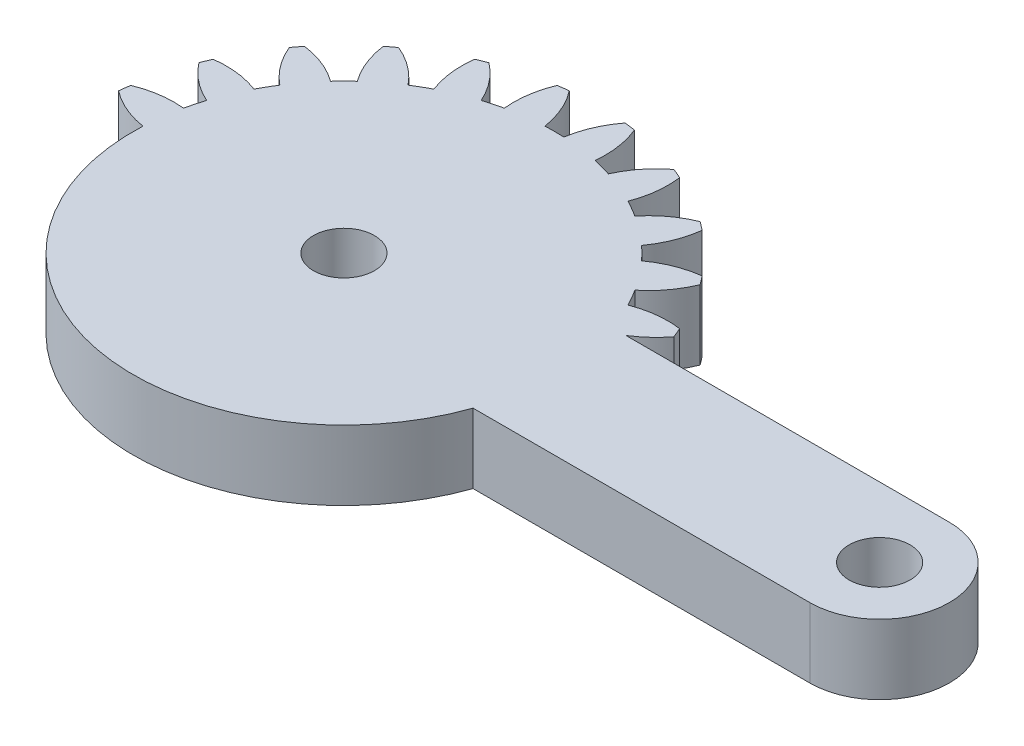
SolidWorks part; units mm, degrees
ref_plane "Front Plane" through (0, 0, 0) normal (0, 0, 1) x (1, 0, 0)
ref_plane "Top Plane" through (0, 0, 0) normal (0, 1, 0) x (1, 0, 0)
ref_plane "Right Plane" through (0, 0, 0) normal (1, 0, 0) x (0, 0, -1)
sketch "Sketch1" plane through (0, 0, 0) normal (0, 1, 0) x (1, 0, 0)
  line L0 (20.6437, 4) -> (2.0816, 4)
  line L1 (2.0816, -4) -> (20.6437, -4)
  arc A0 (2.0816, 4) -> (3.5217, 5.3071) centre (-0.7683, 8.5867) ccw
  arc A1 (3.5217, 5.3071) -> (3.2829, 5.8838) centre (-10.1063, 0) ccw
  arc A2 (3.2829, 5.8838) -> (0.6271, 5.5703) centre (2.5684, 0.5313) ccw
  arc A3 (0.6271, 5.5703) -> (0.0844, 6.5103) centre (-10.1063, 0) ccw
  arc A4 (0.0844, 6.5103) -> (1.6838, 8.6535) centre (-3.3089, 10.711) ccw
  arc A5 (1.6838, 8.6535) -> (1.3038, 9.1487) centre (-10.1063, 0) ccw
  arc A6 (1.3038, 9.1487) -> (-1.1803, 8.1585) centre (1.999, 3.7936) ccw
  arc A7 (-1.1803, 8.1585) -> (-1.9479, 8.926) centre (-10.1063, 0) ccw
  arc A8 (-1.9479, 8.926) -> (-0.9576, 11.4102) centre (-6.3127, 12.1053) ccw
  arc A9 (-0.9576, 11.4102) -> (-1.4528, 11.7901) centre (-10.1063, 0) ccw
  arc A10 (-1.4528, 11.7901) -> (-3.596, 10.1907) centre (0.6046, 6.7975) ccw
  arc A11 (-3.596, 10.1907) -> (-4.5361, 10.7334) centre (-10.1063, 0) ccw
  arc A12 (-4.5361, 10.7334) -> (-4.2225, 13.3892) centre (-9.5751, 12.6747) ccw
  arc A13 (-4.2225, 13.3892) -> (-4.7992, 13.6281) centre (-10.1063, 0) ccw
  arc A14 (-4.7992, 13.6281) -> (-6.4554, 11.5285) centre (-1.5196, 9.3381) ccw
  arc A15 (-6.4554, 11.5285) -> (-7.5039, 11.8094) centre (-10.1063, 0) ccw
  arc A16 (-7.5039, 11.8094) -> (-7.8884, 14.4558) centre (-12.8736, 12.3803) ccw
  arc A17 (-7.8884, 14.4558) -> (-8.5072, 14.5373) centre (-10.1063, 0) ccw
  arc A18 (-8.5072, 14.5373) -> (-9.5636, 12.0806) centre (-4.2291, 11.2423) ccw
  arc A19 (-9.5636, 12.0806) -> (-10.6491, 12.0806) centre (-10.1063, 0) ccw
  arc A20 (-10.6491, 12.0806) -> (-11.7054, 14.5373) centre (-15.9836, 11.2423) ccw
  arc A21 (-11.7054, 14.5373) -> (-12.3243, 14.4558) centre (-10.1063, 0) ccw
  arc A22 (-12.3243, 14.4558) -> (-12.7088, 11.8094) centre (-7.3391, 12.3803) ccw
  arc A23 (-12.7088, 11.8094) -> (-13.7573, 11.5285) centre (-10.1063, 0) ccw
  arc A24 (-13.7573, 11.5285) -> (-15.4135, 13.6281) centre (-18.6931, 9.3381) ccw
  arc A25 (-15.4135, 13.6281) -> (-15.9901, 13.3892) centre (-10.1063, 0) ccw
  arc A26 (-15.9901, 13.3892) -> (-15.6766, 10.7334) centre (-10.6376, 12.6747) ccw
  arc A27 (-15.6766, 10.7334) -> (-16.6166, 10.1907) centre (-10.1063, 0) ccw
  arc A28 (-16.6166, 10.1907) -> (-18.7599, 11.7901) centre (-20.8173, 6.7975) ccw
  arc A29 (-18.7599, 11.7901) -> (-19.255, 11.4102) centre (-10.1063, 0) ccw
  arc A30 (-19.255, 11.4102) -> (-18.2648, 8.926) centre (-13.9, 12.1053) ccw
  arc A31 (-18.2648, 8.926) -> (-19.0324, 8.1585) centre (-10.1063, 0) ccw
  arc A32 (-19.0324, 8.1585) -> (-21.5165, 9.1487) centre (-22.2117, 3.7936) ccw
  arc A33 (-21.5165, 9.1487) -> (-21.8965, 8.6535) centre (-10.1063, 0) ccw
  arc A34 (-21.8965, 8.6535) -> (-20.2971, 6.5103) centre (-16.9038, 10.711) ccw
  arc A35 (-20.2971, 6.5103) -> (-20.8398, 5.5703) centre (-10.1063, 0) ccw
  arc A36 (-20.8398, 5.5703) -> (-23.4956, 5.8838) centre (-22.7811, 0.5313) ccw
  arc A37 (-23.4956, 5.8838) -> (-23.7344, 5.3071) centre (-10.1063, 0) ccw
  arc A38 (-23.7344, 5.3071) -> (-21.6348, 3.6509) centre (-19.4444, 8.5867) ccw
  arc A39 (-21.6348, 3.6509) -> (-21.9157, 2.6025) centre (-10.1063, 0) ccw
  arc A40 (-21.9157, 2.6025) -> (-24.5622, 2.2179) centre (-22.4867, -2.7673) ccw
  arc A41 (-24.5622, 2.2179) -> (-24.6437, 1.5991) centre (-10.1063, 0) ccw
  arc A42 (-24.6437, 1.5991) -> (-22.1869, 0.5427) centre (-21.3486, 5.8773) ccw
  arc A43 (-22.1869, 0.5427) -> (-22.1869, -0.5427) centre (-10.1063, 0) ccw
  arc A44 (-22.1869, -0.5427) -> (-24.6437, -1.5991) centre (-21.3486, -5.8773) ccw
  arc A45 (-24.6437, -1.5991) -> (-24.5622, -2.2179) centre (-10.1063, 0) ccw
  arc A46 (-24.5622, -2.2179) -> (-21.9157, -2.6025) centre (-22.4867, 2.7673) ccw
  arc A47 (-21.9157, -2.6025) -> (-21.6348, -3.6509) centre (-10.1063, 0) ccw
  arc A48 (-21.6348, -3.6509) -> (-23.7344, -5.3071) centre (-19.4444, -8.5867) ccw
  arc A49 (-23.7344, -5.3071) -> (-23.4956, -5.8838) centre (-10.1063, 0) ccw
  arc A50 (-23.4956, -5.8838) -> (-20.8398, -5.5703) centre (-22.7811, -0.5313) ccw
  arc A51 (-20.8398, -5.5703) -> (-20.2971, -6.5103) centre (-10.1063, 0) ccw
  arc A52 (-20.2971, -6.5103) -> (-21.8965, -8.6535) centre (-16.9038, -10.711) ccw
  arc A53 (-21.8965, -8.6535) -> (-21.5165, -9.1487) centre (-10.1063, 0) ccw
  arc A54 (-21.5165, -9.1487) -> (-19.0324, -8.1585) centre (-22.2117, -3.7936) ccw
  arc A55 (-19.0324, -8.1585) -> (-18.2648, -8.926) centre (-10.1063, 0) ccw
  arc A56 (-18.2648, -8.926) -> (-19.255, -11.4102) centre (-13.9, -12.1053) ccw
  arc A57 (-19.255, -11.4102) -> (-18.7599, -11.7901) centre (-10.1063, 0) ccw
  arc A58 (-18.7599, -11.7901) -> (-16.6166, -10.1907) centre (-20.8173, -6.7975) ccw
  arc A59 (-16.6166, -10.1907) -> (-15.6766, -10.7334) centre (-10.1063, 0) ccw
  arc A60 (-15.6766, -10.7334) -> (-15.9901, -13.3892) centre (-10.6376, -12.6747) ccw
  arc A61 (-15.9901, -13.3892) -> (-15.4135, -13.6281) centre (-10.1063, 0) ccw
  arc A62 (-15.4135, -13.6281) -> (-13.7573, -11.5285) centre (-18.6931, -9.3381) ccw
  arc A63 (-13.7573, -11.5285) -> (-12.7088, -11.8094) centre (-10.1063, 0) ccw
  arc A64 (-12.7088, -11.8094) -> (-12.3243, -14.4558) centre (-7.3391, -12.3803) ccw
  arc A65 (-12.3243, -14.4558) -> (-11.7054, -14.5373) centre (-10.1063, 0) ccw
  arc A66 (-11.7054, -14.5373) -> (-10.6491, -12.0806) centre (-15.9836, -11.2423) ccw
  arc A67 (-10.6491, -12.0806) -> (-9.5636, -12.0806) centre (-10.1063, 0) ccw
  arc A68 (-9.5636, -12.0806) -> (-8.5072, -14.5373) centre (-4.2291, -11.2423) ccw
  arc A69 (-8.5072, -14.5373) -> (-7.8884, -14.4558) centre (-10.1063, 0) ccw
  arc A70 (-7.8884, -14.4558) -> (-7.5039, -11.8094) centre (-12.8736, -12.3803) ccw
  arc A71 (-7.5039, -11.8094) -> (-6.4554, -11.5285) centre (-10.1063, 0) ccw
  arc A72 (-6.4554, -11.5285) -> (-4.7992, -13.6281) centre (-1.5196, -9.3381) ccw
  arc A73 (-4.7992, -13.6281) -> (-4.2225, -13.3892) centre (-10.1063, 0) ccw
  arc A74 (-4.2225, -13.3892) -> (-4.5361, -10.7334) centre (-9.5751, -12.6747) ccw
  arc A75 (-4.5361, -10.7334) -> (-3.596, -10.1907) centre (-10.1063, 0) ccw
  arc A76 (-3.596, -10.1907) -> (-1.4528, -11.7901) centre (0.6046, -6.7975) ccw
  arc A77 (-1.4528, -11.7901) -> (-0.9576, -11.4102) centre (-10.1063, 0) ccw
  arc A78 (-0.9576, -11.4102) -> (-1.9479, -8.926) centre (-6.3127, -12.1053) ccw
  arc A79 (-1.9479, -8.926) -> (-1.1803, -8.1585) centre (-10.1063, 0) ccw
  arc A80 (-1.1803, -8.1585) -> (1.3038, -9.1487) centre (1.999, -3.7936) ccw
  arc A81 (1.3038, -9.1487) -> (1.6838, -8.6535) centre (-10.1063, 0) ccw
  arc A82 (1.6838, -8.6535) -> (0.0844, -6.5103) centre (-3.3089, -10.711) ccw
  arc A83 (0.0844, -6.5103) -> (0.6271, -5.5703) centre (-10.1063, 0) ccw
  arc A84 (0.6271, -5.5703) -> (3.2829, -5.8838) centre (2.5684, -0.5313) ccw
  arc A85 (3.2829, -5.8838) -> (3.5217, -5.3071) centre (-10.1063, 0) ccw
  arc A86 (3.5217, -5.3071) -> (2.0816, -4) centre (-0.7683, -8.5867) ccw
  arc A87 (20.6437, -4) -> (20.6437, 4) centre (20.6437, 0) ccw
  circle A88 centre (-10.1063, 0) radius 1.75
  circle A89 centre (20.6437, 0) radius 1.75
  dimension "D1" = 3.5
  dimension "D2" = 3.5
extrude "Boss-Extrude1" add sketch "Sketch1" along normal blind 4
sketch "Sketch2" plane through (0, 4, 0) normal (0, 1, 0) x (1, 0, 0)
  line L0 (2.0816, -4) -> (1.3057, -4)
  line L2 (20.6437, 4) -> (2.0816, 4)
  line L3 (2.0816, -4) -> (20.6437, -4)
  line L4 (20.6437, 4) -> (2.0816, 4)
  line L5 (2.0816, -4) -> (20.6437, -4)
  circle A0 centre (-10.1063, 0) radius 12.0927
  arc A88 (20.6437, -4) -> (20.6437, 4) centre (20.6437, 0) ccw
  arc A89 (2.0816, 4) -> (3.5217, 5.3071) centre (-0.7683, 8.5867) ccw
  arc A90 (3.5217, 5.3071) -> (3.2829, 5.8838) centre (-10.1063, 0) ccw
  arc A91 (3.2829, 5.8838) -> (0.6271, 5.5703) centre (2.5684, 0.5313) ccw
  arc A92 (0.6271, 5.5703) -> (0.0844, 6.5103) centre (-10.1063, 0) ccw
  arc A93 (0.0844, 6.5103) -> (1.6838, 8.6535) centre (-3.3089, 10.711) ccw
  arc A94 (1.6838, 8.6535) -> (1.3038, 9.1487) centre (-10.1063, 0) ccw
  arc A95 (1.3038, 9.1487) -> (-1.1803, 8.1585) centre (1.999, 3.7936) ccw
  arc A96 (-1.1803, 8.1585) -> (-1.9479, 8.926) centre (-10.1063, 0) ccw
  arc A97 (-1.9479, 8.926) -> (-0.9576, 11.4102) centre (-6.3127, 12.1053) ccw
  arc A98 (-0.9576, 11.4102) -> (-1.4528, 11.7901) centre (-10.1063, 0) ccw
  arc A99 (-1.4528, 11.7901) -> (-3.596, 10.1907) centre (0.6046, 6.7975) ccw
  arc A100 (-3.596, 10.1907) -> (-4.5361, 10.7334) centre (-10.1063, 0) ccw
  arc A101 (-4.5361, 10.7334) -> (-4.2225, 13.3892) centre (-9.5751, 12.6747) ccw
  arc A102 (-4.2225, 13.3892) -> (-4.7992, 13.6281) centre (-10.1063, 0) ccw
  arc A103 (-4.7992, 13.6281) -> (-6.4554, 11.5285) centre (-1.5196, 9.3381) ccw
  arc A104 (-6.4554, 11.5285) -> (-7.5039, 11.8094) centre (-10.1063, 0) ccw
  arc A105 (-7.5039, 11.8094) -> (-7.8884, 14.4558) centre (-12.8736, 12.3803) ccw
  arc A106 (-7.8884, 14.4558) -> (-8.5072, 14.5373) centre (-10.1063, 0) ccw
  arc A107 (-8.5072, 14.5373) -> (-9.5636, 12.0806) centre (-4.2291, 11.2423) ccw
  arc A108 (-9.5636, 12.0806) -> (-10.6491, 12.0806) centre (-10.1063, 0) ccw
  arc A109 (-10.6491, 12.0806) -> (-11.7054, 14.5373) centre (-15.9836, 11.2423) ccw
  arc A110 (-11.7054, 14.5373) -> (-12.3243, 14.4558) centre (-10.1063, 0) ccw
  arc A111 (-12.3243, 14.4558) -> (-12.7088, 11.8094) centre (-7.3391, 12.3803) ccw
  arc A112 (-12.7088, 11.8094) -> (-13.7573, 11.5285) centre (-10.1063, 0) ccw
  arc A113 (-13.7573, 11.5285) -> (-15.4135, 13.6281) centre (-18.6931, 9.3381) ccw
  arc A114 (-15.4135, 13.6281) -> (-15.9901, 13.3892) centre (-10.1063, 0) ccw
  arc A115 (-15.9901, 13.3892) -> (-15.6766, 10.7334) centre (-10.6376, 12.6747) ccw
  arc A116 (-15.6766, 10.7334) -> (-16.6166, 10.1907) centre (-10.1063, 0) ccw
  arc A117 (-16.6166, 10.1907) -> (-18.7599, 11.7901) centre (-20.8173, 6.7975) ccw
  arc A118 (-18.7599, 11.7901) -> (-19.255, 11.4102) centre (-10.1063, 0) ccw
  arc A119 (-19.255, 11.4102) -> (-18.2648, 8.926) centre (-13.9, 12.1053) ccw
  arc A120 (-18.2648, 8.926) -> (-19.0324, 8.1585) centre (-10.1063, 0) ccw
  arc A121 (-19.0324, 8.1585) -> (-21.5165, 9.1487) centre (-22.2117, 3.7936) ccw
  arc A122 (-21.5165, 9.1487) -> (-21.8965, 8.6535) centre (-10.1063, 0) ccw
  arc A123 (-21.8965, 8.6535) -> (-20.2971, 6.5103) centre (-16.9038, 10.711) ccw
  arc A124 (-20.2971, 6.5103) -> (-20.8398, 5.5703) centre (-10.1063, 0) ccw
  arc A125 (-20.8398, 5.5703) -> (-23.4956, 5.8838) centre (-22.7811, 0.5313) ccw
  arc A126 (-23.4956, 5.8838) -> (-23.7344, 5.3071) centre (-10.1063, 0) ccw
  arc A127 (-23.7344, 5.3071) -> (-21.6348, 3.6509) centre (-19.4444, 8.5867) ccw
  arc A128 (-21.6348, 3.6509) -> (-21.9157, 2.6025) centre (-10.1063, 0) ccw
  arc A129 (-21.9157, 2.6025) -> (-24.5622, 2.2179) centre (-22.4867, -2.7673) ccw
  arc A130 (-24.5622, 2.2179) -> (-24.6437, 1.5991) centre (-10.1063, 0) ccw
  arc A131 (-24.6437, 1.5991) -> (-22.1869, 0.5427) centre (-21.3486, 5.8773) ccw
  arc A132 (-22.1869, 0.5427) -> (-22.1869, -0.5427) centre (-10.1063, 0) ccw
  arc A133 (-22.1869, -0.5427) -> (-24.6437, -1.5991) centre (-21.3486, -5.8773) ccw
  arc A134 (-24.6437, -1.5991) -> (-24.5622, -2.2179) centre (-10.1063, 0) ccw
  arc A135 (-24.5622, -2.2179) -> (-21.9157, -2.6025) centre (-22.4867, 2.7673) ccw
  arc A136 (-21.9157, -2.6025) -> (-21.6348, -3.6509) centre (-10.1063, 0) ccw
  arc A137 (-21.6348, -3.6509) -> (-23.7344, -5.3071) centre (-19.4444, -8.5867) ccw
  arc A138 (-23.7344, -5.3071) -> (-23.4956, -5.8838) centre (-10.1063, 0) ccw
  arc A139 (-23.4956, -5.8838) -> (-20.8398, -5.5703) centre (-22.7811, -0.5313) ccw
  arc A140 (-20.8398, -5.5703) -> (-20.2971, -6.5103) centre (-10.1063, 0) ccw
  arc A141 (-20.2971, -6.5103) -> (-21.8965, -8.6535) centre (-16.9038, -10.711) ccw
  arc A142 (-21.8965, -8.6535) -> (-21.5165, -9.1487) centre (-10.1063, 0) ccw
  arc A143 (-21.5165, -9.1487) -> (-19.0324, -8.1585) centre (-22.2117, -3.7936) ccw
  arc A144 (-19.0324, -8.1585) -> (-18.2648, -8.926) centre (-10.1063, 0) ccw
  arc A145 (-18.2648, -8.926) -> (-19.255, -11.4102) centre (-13.9, -12.1053) ccw
  arc A146 (-19.255, -11.4102) -> (-18.7599, -11.7901) centre (-10.1063, 0) ccw
  arc A147 (-18.7599, -11.7901) -> (-16.6166, -10.1907) centre (-20.8173, -6.7975) ccw
  arc A148 (-16.6166, -10.1907) -> (-15.6766, -10.7334) centre (-10.1063, 0) ccw
  arc A149 (-15.6766, -10.7334) -> (-15.9901, -13.3892) centre (-10.6376, -12.6747) ccw
  arc A150 (-15.9901, -13.3892) -> (-15.4135, -13.6281) centre (-10.1063, 0) ccw
  arc A151 (-15.4135, -13.6281) -> (-13.7573, -11.5285) centre (-18.6931, -9.3381) ccw
  arc A152 (-13.7573, -11.5285) -> (-12.7088, -11.8094) centre (-10.1063, 0) ccw
  arc A153 (-12.7088, -11.8094) -> (-12.3243, -14.4558) centre (-7.3391, -12.3803) ccw
  arc A154 (-12.3243, -14.4558) -> (-11.7054, -14.5373) centre (-10.1063, 0) ccw
  arc A155 (-11.7054, -14.5373) -> (-10.6491, -12.0806) centre (-15.9836, -11.2423) ccw
  arc A156 (-10.6491, -12.0806) -> (-9.5636, -12.0806) centre (-10.1063, 0) ccw
  arc A157 (-9.5636, -12.0806) -> (-8.5072, -14.5373) centre (-4.2291, -11.2423) ccw
  arc A158 (-8.5072, -14.5373) -> (-7.8884, -14.4558) centre (-10.1063, 0) ccw
  arc A159 (-7.8884, -14.4558) -> (-7.5039, -11.8094) centre (-12.8736, -12.3803) ccw
  arc A160 (-7.5039, -11.8094) -> (-6.4554, -11.5285) centre (-10.1063, 0) ccw
  arc A161 (-6.4554, -11.5285) -> (-4.7992, -13.6281) centre (-1.5196, -9.3381) ccw
  arc A162 (-4.7992, -13.6281) -> (-4.2225, -13.3892) centre (-10.1063, 0) ccw
  arc A163 (-4.2225, -13.3892) -> (-4.5361, -10.7334) centre (-9.5751, -12.6747) ccw
  arc A164 (-4.5361, -10.7334) -> (-3.596, -10.1907) centre (-10.1063, 0) ccw
  arc A165 (-3.596, -10.1907) -> (-1.4528, -11.7901) centre (0.6046, -6.7975) ccw
  arc A166 (-1.4528, -11.7901) -> (-0.9576, -11.4102) centre (-10.1063, 0) ccw
  arc A167 (-0.9576, -11.4102) -> (-1.9479, -8.926) centre (-6.3127, -12.1053) ccw
  arc A168 (-1.9479, -8.926) -> (-1.1803, -8.1585) centre (-10.1063, 0) ccw
  arc A169 (-1.1803, -8.1585) -> (1.3038, -9.1487) centre (1.999, -3.7936) ccw
  arc A170 (1.3038, -9.1487) -> (1.6838, -8.6535) centre (-10.1063, 0) ccw
  arc A171 (1.6838, -8.6535) -> (0.0844, -6.5103) centre (-3.3089, -10.711) ccw
  arc A172 (0.0844, -6.5103) -> (0.6271, -5.5703) centre (-10.1063, 0) ccw
  arc A173 (0.6271, -5.5703) -> (3.2829, -5.8838) centre (2.5684, -0.5313) ccw
  arc A174 (3.2829, -5.8838) -> (3.5217, -5.3071) centre (-10.1063, 0) ccw
  arc A175 (3.5217, -5.3071) -> (2.0816, -4) centre (-0.7683, -8.5867) ccw
  arc A176 (20.6437, -4) -> (20.6437, 4) centre (20.6437, 0) ccw
  arc A177 (2.0816, 4) -> (3.5217, 5.3071) centre (-0.7683, 8.5867) ccw
  arc A178 (3.5217, 5.3071) -> (3.2829, 5.8838) centre (-10.1063, 0) ccw
  arc A179 (3.2829, 5.8838) -> (0.6271, 5.5703) centre (2.5684, 0.5313) ccw
  arc A180 (0.6271, 5.5703) -> (0.0844, 6.5103) centre (-10.1063, 0) ccw
  arc A181 (0.0844, 6.5103) -> (1.6838, 8.6535) centre (-3.3089, 10.711) ccw
  arc A182 (1.6838, 8.6535) -> (1.3038, 9.1487) centre (-10.1063, 0) ccw
  arc A183 (1.3038, 9.1487) -> (-1.1803, 8.1585) centre (1.999, 3.7936) ccw
  arc A184 (-1.1803, 8.1585) -> (-1.9479, 8.926) centre (-10.1063, 0) ccw
  arc A185 (-1.9479, 8.926) -> (-0.9576, 11.4102) centre (-6.3127, 12.1053) ccw
  arc A186 (-0.9576, 11.4102) -> (-1.4528, 11.7901) centre (-10.1063, 0) ccw
  arc A187 (-1.4528, 11.7901) -> (-3.596, 10.1907) centre (0.6046, 6.7975) ccw
  arc A188 (-3.596, 10.1907) -> (-4.5361, 10.7334) centre (-10.1063, 0) ccw
  arc A189 (-4.5361, 10.7334) -> (-4.2225, 13.3892) centre (-9.5751, 12.6747) ccw
  arc A190 (-4.2225, 13.3892) -> (-4.7992, 13.6281) centre (-10.1063, 0) ccw
  arc A191 (-4.7992, 13.6281) -> (-6.4554, 11.5285) centre (-1.5196, 9.3381) ccw
  arc A192 (-6.4554, 11.5285) -> (-7.5039, 11.8094) centre (-10.1063, 0) ccw
  arc A193 (-7.5039, 11.8094) -> (-7.8884, 14.4558) centre (-12.8736, 12.3803) ccw
  arc A194 (-7.8884, 14.4558) -> (-8.5072, 14.5373) centre (-10.1063, 0) ccw
  arc A195 (-8.5072, 14.5373) -> (-9.5636, 12.0806) centre (-4.2291, 11.2423) ccw
  arc A196 (-9.5636, 12.0806) -> (-10.6491, 12.0806) centre (-10.1063, 0) ccw
  arc A197 (-10.6491, 12.0806) -> (-11.7054, 14.5373) centre (-15.9836, 11.2423) ccw
  arc A198 (-11.7054, 14.5373) -> (-12.3243, 14.4558) centre (-10.1063, 0) ccw
  arc A199 (-12.3243, 14.4558) -> (-12.7088, 11.8094) centre (-7.3391, 12.3803) ccw
  arc A200 (-12.7088, 11.8094) -> (-13.7573, 11.5285) centre (-10.1063, 0) ccw
  arc A201 (-13.7573, 11.5285) -> (-15.4135, 13.6281) centre (-18.6931, 9.3381) ccw
  arc A202 (-15.4135, 13.6281) -> (-15.9901, 13.3892) centre (-10.1063, 0) ccw
  arc A203 (-15.9901, 13.3892) -> (-15.6766, 10.7334) centre (-10.6376, 12.6747) ccw
  arc A204 (-15.6766, 10.7334) -> (-16.6166, 10.1907) centre (-10.1063, 0) ccw
  arc A205 (-16.6166, 10.1907) -> (-18.7599, 11.7901) centre (-20.8173, 6.7975) ccw
  arc A206 (-18.7599, 11.7901) -> (-19.255, 11.4102) centre (-10.1063, 0) ccw
  arc A207 (-19.255, 11.4102) -> (-18.2648, 8.926) centre (-13.9, 12.1053) ccw
  arc A208 (-18.2648, 8.926) -> (-19.0324, 8.1585) centre (-10.1063, 0) ccw
  arc A209 (-19.0324, 8.1585) -> (-21.5165, 9.1487) centre (-22.2117, 3.7936) ccw
  arc A210 (-21.5165, 9.1487) -> (-21.8965, 8.6535) centre (-10.1063, 0) ccw
  arc A211 (-21.8965, 8.6535) -> (-20.2971, 6.5103) centre (-16.9038, 10.711) ccw
  arc A212 (-20.2971, 6.5103) -> (-20.8398, 5.5703) centre (-10.1063, 0) ccw
  arc A213 (-20.8398, 5.5703) -> (-23.4956, 5.8838) centre (-22.7811, 0.5313) ccw
  arc A214 (-23.4956, 5.8838) -> (-23.7344, 5.3071) centre (-10.1063, 0) ccw
  arc A215 (-23.7344, 5.3071) -> (-21.6348, 3.6509) centre (-19.4444, 8.5867) ccw
  arc A216 (-21.6348, 3.6509) -> (-21.9157, 2.6025) centre (-10.1063, 0) ccw
  arc A217 (-21.9157, 2.6025) -> (-24.5622, 2.2179) centre (-22.4867, -2.7673) ccw
  arc A218 (-24.5622, 2.2179) -> (-24.6437, 1.5991) centre (-10.1063, 0) ccw
  arc A219 (-24.6437, 1.5991) -> (-22.1869, 0.5427) centre (-21.3486, 5.8773) ccw
  arc A220 (-22.1869, 0.5427) -> (-22.1869, -0.5427) centre (-10.1063, 0) ccw
  arc A221 (-22.1869, -0.5427) -> (-24.6437, -1.5991) centre (-21.3486, -5.8773) ccw
  arc A222 (-24.6437, -1.5991) -> (-24.5622, -2.2179) centre (-10.1063, 0) ccw
  arc A223 (-24.5622, -2.2179) -> (-21.9157, -2.6025) centre (-22.4867, 2.7673) ccw
  arc A224 (-21.9157, -2.6025) -> (-21.6348, -3.6509) centre (-10.1063, 0) ccw
  arc A225 (-21.6348, -3.6509) -> (-23.7344, -5.3071) centre (-19.4444, -8.5867) ccw
  arc A226 (-23.7344, -5.3071) -> (-23.4956, -5.8838) centre (-10.1063, 0) ccw
  arc A227 (-23.4956, -5.8838) -> (-20.8398, -5.5703) centre (-22.7811, -0.5313) ccw
  arc A228 (-20.8398, -5.5703) -> (-20.2971, -6.5103) centre (-10.1063, 0) ccw
  arc A229 (-20.2971, -6.5103) -> (-21.8965, -8.6535) centre (-16.9038, -10.711) ccw
  arc A230 (-21.8965, -8.6535) -> (-21.5165, -9.1487) centre (-10.1063, 0) ccw
  arc A231 (-21.5165, -9.1487) -> (-19.0324, -8.1585) centre (-22.2117, -3.7936) ccw
  arc A232 (-19.0324, -8.1585) -> (-18.2648, -8.926) centre (-10.1063, 0) ccw
  arc A233 (-18.2648, -8.926) -> (-19.255, -11.4102) centre (-13.9, -12.1053) ccw
  arc A234 (-19.255, -11.4102) -> (-18.7599, -11.7901) centre (-10.1063, 0) ccw
  arc A235 (-18.7599, -11.7901) -> (-16.6166, -10.1907) centre (-20.8173, -6.7975) ccw
  arc A236 (-16.6166, -10.1907) -> (-15.6766, -10.7334) centre (-10.1063, 0) ccw
  arc A237 (-15.6766, -10.7334) -> (-15.9901, -13.3892) centre (-10.6376, -12.6747) ccw
  arc A238 (-15.9901, -13.3892) -> (-15.4135, -13.6281) centre (-10.1063, 0) ccw
  arc A239 (-15.4135, -13.6281) -> (-13.7573, -11.5285) centre (-18.6931, -9.3381) ccw
  arc A240 (-13.7573, -11.5285) -> (-12.7088, -11.8094) centre (-10.1063, 0) ccw
  arc A241 (-12.7088, -11.8094) -> (-12.3243, -14.4558) centre (-7.3391, -12.3803) ccw
  arc A242 (-12.3243, -14.4558) -> (-11.7054, -14.5373) centre (-10.1063, 0) ccw
  arc A243 (-11.7054, -14.5373) -> (-10.6491, -12.0806) centre (-15.9836, -11.2423) ccw
  arc A244 (-10.6491, -12.0806) -> (-9.5636, -12.0806) centre (-10.1063, 0) ccw
  arc A245 (-9.5636, -12.0806) -> (-8.5072, -14.5373) centre (-4.2291, -11.2423) ccw
  arc A246 (-8.5072, -14.5373) -> (-7.8884, -14.4558) centre (-10.1063, 0) ccw
  arc A247 (-7.8884, -14.4558) -> (-7.5039, -11.8094) centre (-12.8736, -12.3803) ccw
  arc A248 (-7.5039, -11.8094) -> (-6.4554, -11.5285) centre (-10.1063, 0) ccw
  arc A249 (-6.4554, -11.5285) -> (-4.7992, -13.6281) centre (-1.5196, -9.3381) ccw
  arc A250 (-4.7992, -13.6281) -> (-4.2225, -13.3892) centre (-10.1063, 0) ccw
  arc A251 (-4.2225, -13.3892) -> (-4.5361, -10.7334) centre (-9.5751, -12.6747) ccw
  arc A252 (-4.5361, -10.7334) -> (-3.596, -10.1907) centre (-10.1063, 0) ccw
  arc A253 (-3.596, -10.1907) -> (-1.4528, -11.7901) centre (0.6046, -6.7975) ccw
  arc A254 (-1.4528, -11.7901) -> (-0.9576, -11.4102) centre (-10.1063, 0) ccw
  arc A255 (-0.9576, -11.4102) -> (-1.9479, -8.926) centre (-6.3127, -12.1053) ccw
  arc A256 (-1.9479, -8.926) -> (-1.1803, -8.1585) centre (-10.1063, 0) ccw
  arc A257 (-1.1803, -8.1585) -> (1.3038, -9.1487) centre (1.999, -3.7936) ccw
  arc A258 (1.3038, -9.1487) -> (1.6838, -8.6535) centre (-10.1063, 0) ccw
  arc A259 (1.6838, -8.6535) -> (0.0844, -6.5103) centre (-3.3089, -10.711) ccw
  arc A260 (0.0844, -6.5103) -> (0.6271, -5.5703) centre (-10.1063, 0) ccw
  arc A261 (0.6271, -5.5703) -> (3.2829, -5.8838) centre (2.5684, -0.5313) ccw
  arc A262 (3.2829, -5.8838) -> (3.5217, -5.3071) centre (-10.1063, 0) ccw
  arc A263 (3.5217, -5.3071) -> (2.0816, -4) centre (-0.7683, -8.5867) ccw
  dimension "D1" = 0
extrude "Cut-Extrude1" cut sketch "Sketch2" against normal blind 10 contours A222 A223 A0 A221 | A226 A227 A0 A225 | A230 A231 A0 A229 | A234 A235 A0 A233 | A238 A239 A0 A237 | A242 A243 A0 A241 | A246 A247 A0 A245 | A250 A251 A0 A249 | A254 A255 A0 A253 | A258 A259 A0 A257 | A262 A263 L0 A0 A261
